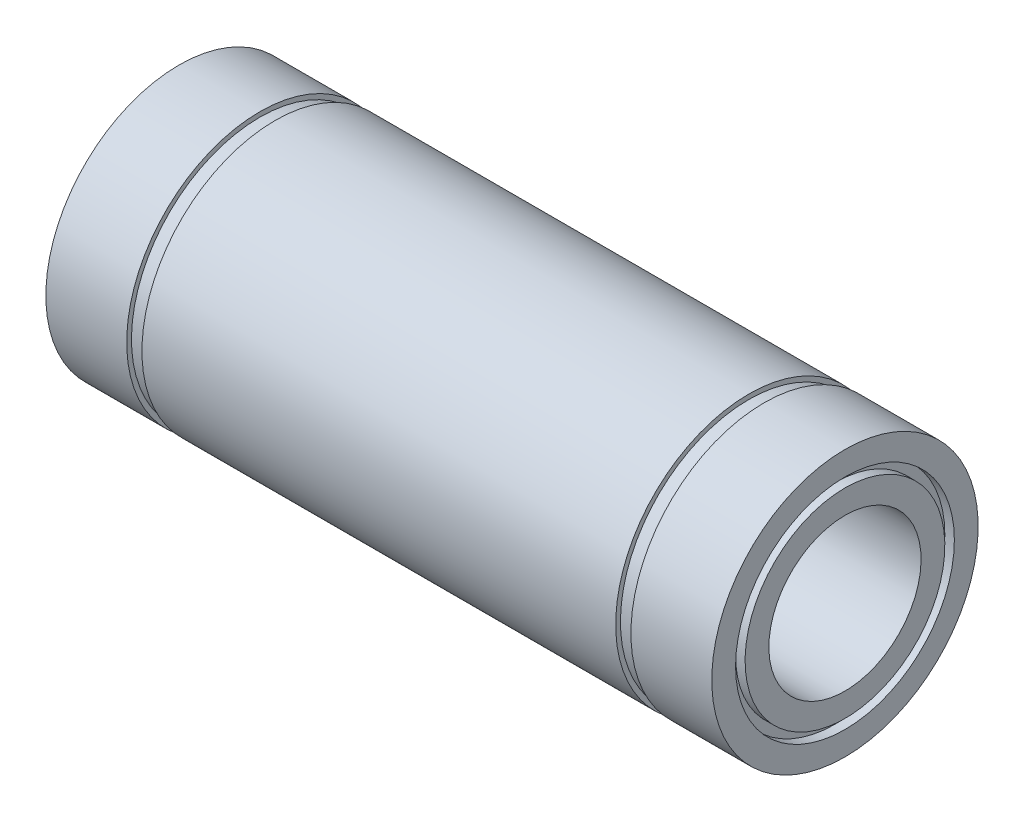
SolidWorks part; units mm, degrees
material "Ст3сп ГОСТ 535-2005"
ref_plane "Plano frontal" through (0, 0, 0) normal (0, 0, 1) x (1, 0, 0)
ref_plane "Plano superior" through (0, 0, 0) normal (0, 1, 0) x (1, 0, 0)
ref_plane "Plano direito" through (0, 0, 0) normal (1, 0, 0) x (0, 0, -1)
sketch "Esboço1" plane through (0, 0, 0) normal (0, 0, 1) x (1, 0, 0)
  line L0 (-35, 14) -> (-26.5, 14)
  line L1 (-26.5, 14) -> (-26.5, 13.5)
  line L2 (-26.5, 13.5) -> (-24.9, 13.5)
  line L3 (-24.9, 13.5) -> (-24.9, 14)
  line L4 (-24.9, 14) -> (24.9, 14)
  line L5 (24.9, 14) -> (24.9, 13.5)
  line L6 (24.9, 13.5) -> (26.5, 13.5)
  line L7 (26.5, 13.5) -> (26.5, 14)
  line L8 (26.5, 14) -> (35, 14)
  line L9 (35, 14) -> (35, 11.5)
  line L10 (35, 8) -> (-35, 8)
  line L11 (-35, 8) -> (-35, 10.5)
  line L12 (0, 8) -> (0, 0) construction
  line L13 (0, 0) -> (-86.5, 0) construction
  line L14 (-35, 11.5) -> (-35, 14)
  line L15 (-35, 11.5) -> (-34, 11.5)
  line L16 (35, 10.5) -> (35, 8)
  line L17 (-34, 11.5) -> (-34, 10.5)
  line L18 (-34, 10.5) -> (-35, 10.5)
  line L19 (35, 11.5) -> (34, 11.5)
  line L21 (35, 10.5) -> (34, 10.5)
  line L22 (34, 11.5) -> (34, 10.5)
  dimension "D1" = 70
  dimension "D2" = 53
  dimension "D3" = 1.6
  dimension "D4" = 16
  dimension "D5" = 28
  dimension "D6" = 27
  dimension "D7" = 1
  dimension "D8" = 1
  dimension "D9" = 1
  dimension "D10" = 1
revolve "Revolução1" add sketch "Esboço1" angle 360 about L13
